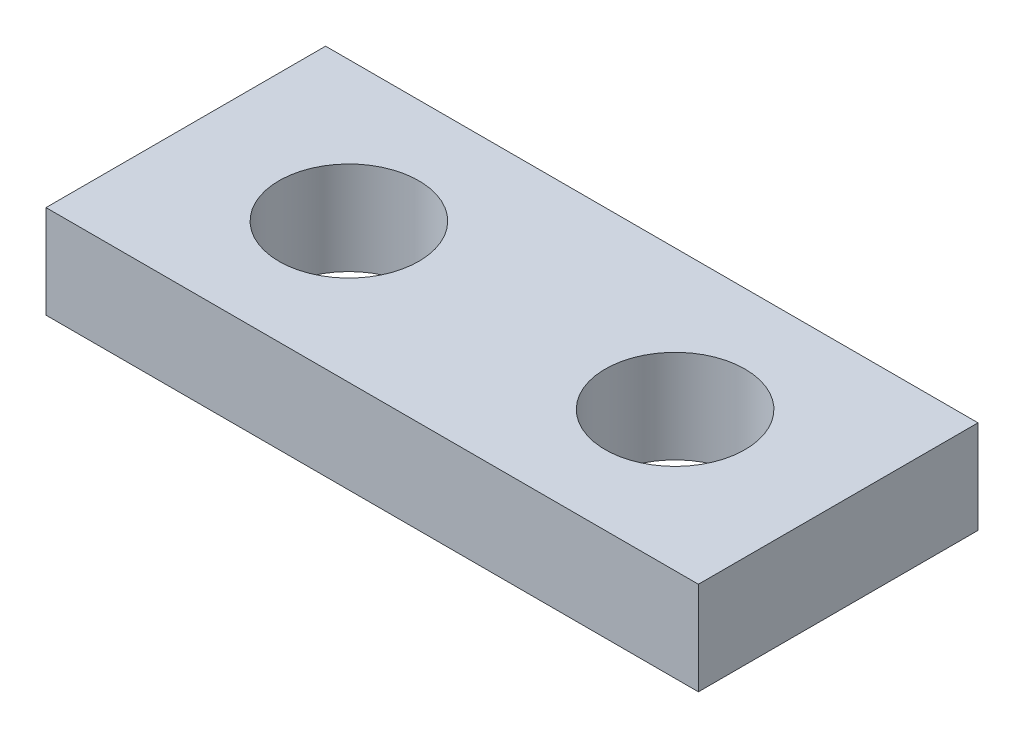
SolidWorks part; units mm, degrees
ref_plane "Front Plane" through (0, 0, 0) normal (0, 0, 1) x (1, 0, 0)
ref_plane "Top Plane" through (0, 0, 0) normal (0, 1, 0) x (1, 0, 0)
ref_plane "Right Plane" through (0, 0, 0) normal (1, 0, 0) x (0, 0, -1)
sketch "Sketch1" plane through (0, 0, 0) normal (0, 1, 0) x (1, 0, 0)
  line L0 (7, 6) -> (7, -4.2492) construction
  line L1 (0, 0) -> (14, 0)
  line L2 (0, 0) -> (0, 6)
  line L3 (0, 6) -> (14, 6)
  line L4 (14, 0) -> (14, 6)
  circle A0 centre (3.5, 3) radius 1.5
  circle A1 centre (10.5, 3) radius 1.5
  dimension "D3" = 3
  dimension "D1" = 6
  dimension "D2" = 14
  dimension "D4" = 3.5
  dimension "D5" = 3
extrude "Boss-Extrude1" add sketch "Sketch1" along normal blind 2
